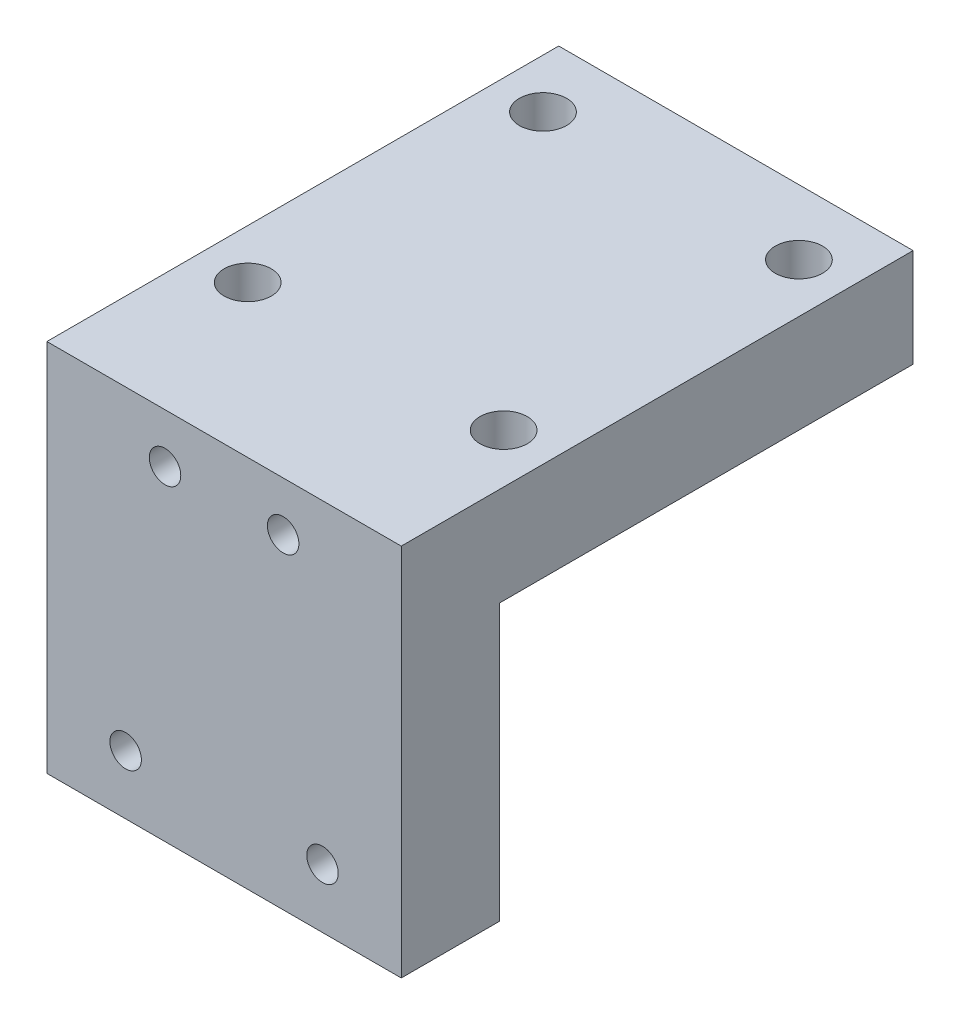
SolidWorks part; units mm, degrees
ref_plane "Front Plane" through (0, 0, 0) normal (0, 0, 1) x (1, 0, 0)
ref_plane "Top Plane" through (0, 0, 0) normal (0, 1, 0) x (1, 0, 0)
ref_plane "Right Plane" through (0, 0, 0) normal (1, 0, 0) x (0, 0, -1)
sketch "Sketch1" plane through (0, 0, 0) normal (0, 1, 0) x (1, 0, 0)
  line L1 (0, 0) -> (18, 0)
  line L2 (0, 0) -> (0, 26)
  line L3 (0, 26) -> (18, 26)
  line L4 (18, 0) -> (18, 26)
  dimension "D1" = 18
  dimension "D2" = 26
extrude "Boss-Extrude1" add sketch "Sketch1" along normal blind 5
sketch "Sketch2" plane through (0, 0, 0) normal (0, -1, 0) x (1, 0, 0)
  line L0 (0, -26) -> (0, 0) construction
  line L1 (18, 0) -> (0, 0)
  line L2 (18, 0) -> (18, -5)
  line L3 (18, -5) -> (0, -5)
  line L4 (0, 0) -> (0, -5)
  dimension "D1" = 5
extrude "Boss-Extrude2" add sketch "Sketch2" along normal blind 14
hole_wizard "M2 Clearance Hole1" positions "3DSketch2" profile "Sketch5" hole size "M2" standard "ISO"
sketch3d "3DSketch2"
  line L1 (2.5, 5, -7.7) -> (2.5, 5, -22.7) construction
  line L2 (2.5, 5, -7.7) -> (15.5, 5, -7.7) construction
  line L3 (15.5, 5, -7.7) -> (15.5, 5, -22.7) construction
  line L4 (2.5, 5, -22.7) -> (15.5, 5, -22.7) construction
  line L7 (0, 5, -26) -> (0, 5, 0) construction
  line L8 (0, 5, 0) -> (18, 5, 0) construction
  point P87 (2.5, 5, -22.7)
  point P89 (15.5, 5, -22.7)
  point P95 (2.5, 5, -7.7)
  point P97 (15.5, 5, -7.7)
  point P111 (2.5, 5, -22.7)
  point P113 (15.5, 5, -22.7)
  dimension "D1" = 2.5
  dimension "D2" = 15
  dimension "D3" = 7.7
  dimension "D4" = 13
sketch "Sketch5" plane through (2.5, 5, -7.7) normal (1, 0, 0) x (0, 0, 1)
  line L0 (0, 0) -> (0, 10.721)
  line L1 (0, 10.721) -> (1.2, 10)
  line L2 (1.2, 10) -> (1.2, 0)
  line L5 (1.2, 0) -> (0, 0)
  line L10 (0, 10.721) -> (-1.2, 10) construction
  line L11 (0, -6.35) -> (0, 107.95) construction
  dimension "Hole Dia." = 2.4
  dimension "Hole Depth" = 10
  dimension "Drill Angle" = 118
hole_wizard "M2 Tapped Hole1" positions "Sketch7" profile "Sketch6" tap size "M2" standard "ISO"
sketch "Sketch7" plane through (0, 0, 0) normal (0, 0, 1) x (1, 0, 0)
  line L0 (0, 2.5) -> (18, 2.5) construction
  line L1 (0, 5) -> (0, -14) construction
  line L2 (18, 5) -> (18, -14) construction
  line L4 (0, 5) -> (18, 5) construction
  line L5 (0, -11) -> (18, -11) construction
  line L7 (18, -14) -> (0, -14) construction
  point P0 (6, 2.5)
  point P1 (12, 2.5)
  point P3 (4, -11)
  point P5 (14, -11)
  dimension "D1" = 2.5
  dimension "D2" = 6
  dimension "D3" = 6
  dimension "D4" = 4
  dimension "D5" = 4
  dimension "D6" = 3
sketch "Sketch6" plane through (6, 2.5, 0) normal (1, 0, 0) x (0, -1, 0)
  line L0 (0, 0) -> (0, 11.6807)
  line L1 (0, 11.6807) -> (0.8, 11.2)
  line L2 (0.8, 11.2) -> (0.8, 0)
  line L5 (0.8, 0) -> (0, 0)
  line L10 (0, 11.6807) -> (-0.8, 11.2) construction
  line L11 (0, -6.35) -> (0, 107.95) construction
  dimension "Tap Drill Dia." = 1.6
  dimension "Tap Drill Depth" = 11.2
  dimension "Drill Angle" = 118
cosmetic thread "Hole Thread1" parameters "D1"=5, "D2"=2
cosmetic thread "Hole Thread2" parameters "D1"=5, "D2"=2
cosmetic thread "Hole Thread3" parameters "D1"=10, "D2"=2
cosmetic thread "Hole Thread4" parameters "D1"=10, "D2"=2
